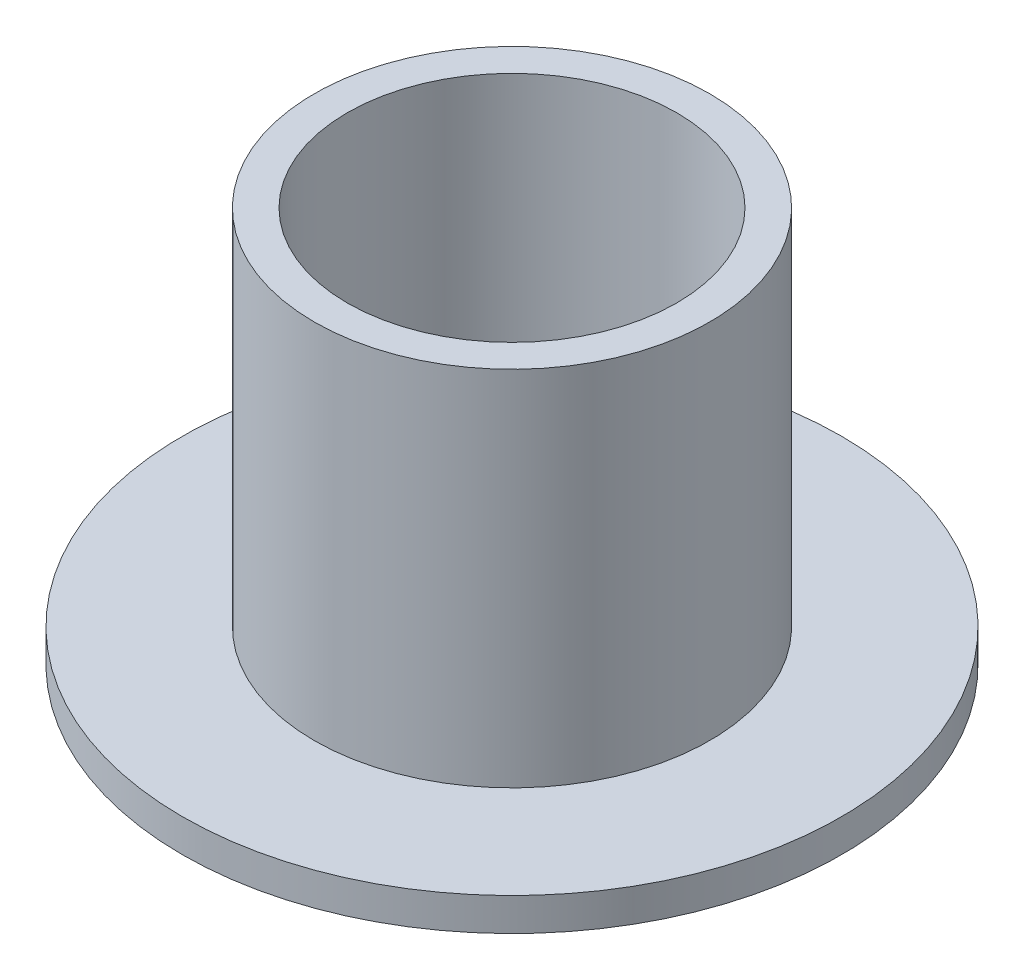
SolidWorks part; units mm, degrees
ref_plane "Vorne" through (0, 0, 0) normal (0, 0, 1) x (1, 0, 0)
ref_plane "Oben" through (0, 0, 0) normal (0, 1, 0) x (1, 0, 0)
ref_plane "Rechts" through (0, 0, 0) normal (1, 0, 0) x (0, 0, -1)
sketch "Skizze1" plane through (0, 0, 0) normal (0, 1, 0) x (1, 0, 0)
  circle A0 centre (0, 0) radius 2.5
  circle A1 centre (0, 0) radius 3
  dimension "D1" = 5
  dimension "D2" = 6
extrude "Aufsatz-Linear austragen1" add sketch "Skizze1" along normal blind 6
sketch "Skizze2" plane through (0, 0, 0) normal (0, 1, 0) x (1, 0, 0)
  circle A0 centre (0, 0) radius 3 construction
  circle A1 centre (0, 0) radius 3
  circle A2 centre (0, 0) radius 5
  dimension "D1" = 10
extrude "Aufsatz-Linear austragen2" add sketch "Skizze2" along normal blind 0.5
